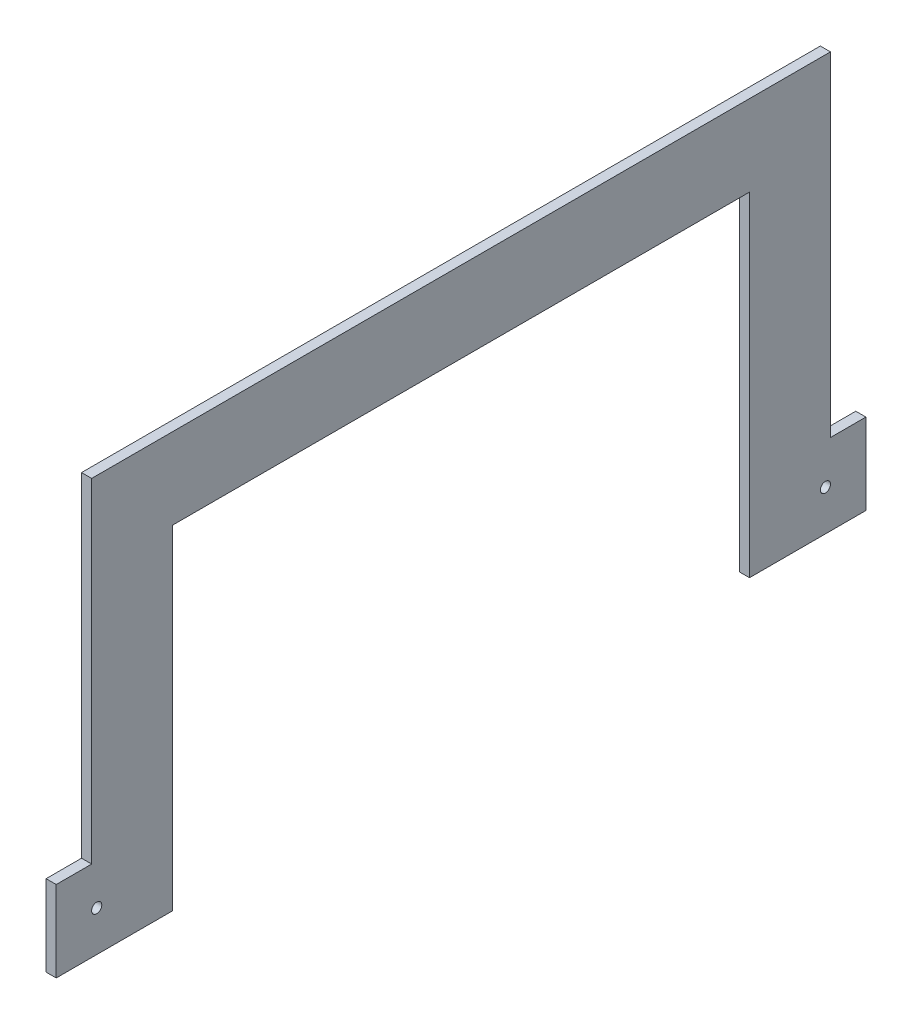
SolidWorks part; units mm, degrees
ref_plane "Front Plane" through (0, 0, 0) normal (0, 0, 1) x (1, 0, 0)
ref_plane "Top Plane" through (0, 0, 0) normal (0, 1, 0) x (1, 0, 0)
ref_plane "Right Plane" through (0, 0, 0) normal (1, 0, 0) x (0, 0, -1)
sketch "Sketch1" plane through (0, 0, 0) normal (1, 0, 0) x (0, 0, -1)
  line L0 (-90.4875, 0) -> (90.4875, 0)
  line L1 (90.4875, 0) -> (90.4875, -104.775)
  line L2 (90.4875, -104.775) -> (127, -104.775)
  line L3 (127, -104.775) -> (127, -79.375)
  line L4 (127, -79.375) -> (115.8875, -79.375)
  line L5 (115.8875, -79.375) -> (115.8875, 25.4)
  line L6 (115.8875, 25.4) -> (-115.8875, 25.4)
  line L7 (-115.8875, 25.4) -> (-115.8875, -79.375)
  line L8 (-115.8875, -79.375) -> (-127, -79.375)
  line L9 (-127, -79.375) -> (-127, -104.775)
  line L10 (-127, -104.775) -> (-90.4875, -104.775)
  line L11 (-90.4875, -104.775) -> (-90.4875, 0)
  line L12 (90.4875, 0) -> (115.8875, 0) construction
  line L13 (-90.4875, 0) -> (-115.8875, 0) construction
  line L14 (-115.8875, -79.375) -> (-115.8875, -104.775) construction
  line L15 (115.8875, -79.375) -> (115.8875, -104.775) construction
  line L16 (90.4875, 0) -> (90.4875, 25.4) construction
  point P4 (0, 0)
  dimension "D1" = 25.4
  dimension "D2" = 254
  dimension "D3" = 180.975
  dimension "D4" = 104.775
extrude "Boss-Extrude1" add sketch "Sketch1" along normal blind 3.175
sketch "Sketch2" plane through (3.175, 0, 0) normal (1, 0, 0) x (0, 0, -1)
  line L0 (-114.3, -92.075) -> (-127, -92.075) construction
  line L1 (-127, -79.375) -> (-127, -104.775) construction
  line L2 (114.3, -92.075) -> (127, -92.075) construction
  line L3 (127, -104.775) -> (127, -79.375) construction
  circle A0 centre (-114.3, -92.075) radius 1.5875
  circle A1 centre (114.3, -92.075) radius 1.5875
  dimension "D1" = 3.175
  dimension "D2" = 228.6
extrude "Cut-Extrude1" cut sketch "Sketch2" against normal through all
equation "\"Thick\"= \"in\""
